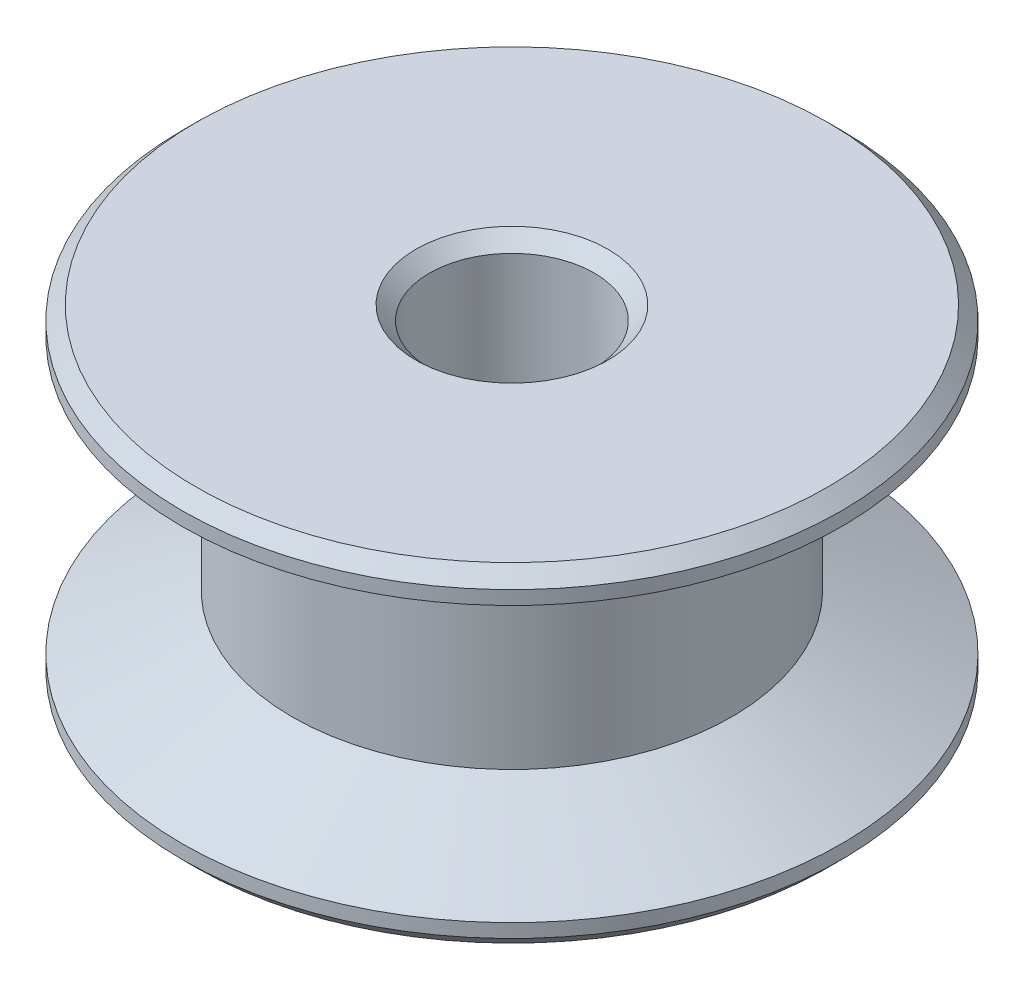
SolidWorks part; units mm, degrees
ref_plane "Front Plane" through (0, 0, 0) normal (0, 0, 1) x (1, 0, 0)
ref_plane "Top Plane" through (0, 0, 0) normal (0, 1, 0) x (1, 0, 0)
ref_plane "Right Plane" through (0, 0, 0) normal (1, 0, 0) x (0, 0, -1)
sketch "Sketch1" plane through (0, 0, 0) normal (0, 0, 1) x (1, 0, 0)
  line L0 (0, 0) -> (9.525, 0)
  line L1 (9.525, 0) -> (9.525, 0.7937)
  line L2 (9.525, 0.7937) -> (6.35, 2.3812)
  line L3 (6.35, 2.3812) -> (6.35, 7.1437)
  line L4 (6.35, 7.1437) -> (9.525, 8.7312)
  line L5 (9.525, 8.7312) -> (9.525, 9.525)
  line L6 (9.525, 9.525) -> (0, 9.525)
  line L7 (0, 9.525) -> (0, 0)
  dimension "D1" = 6.35
  dimension "D2" = 3.175
  dimension "D3" = 3.175
  dimension "D4" = 0.7937
  dimension "D5" = 1.5875
  dimension "D6" = 4.7625
  dimension "D7" = 1.5875
  dimension "D8" = 0.7937
revolve "Revolve1" add sketch "Sketch1" angle 360 about L7
sketch "Sketch2" plane through (0, 9.525, 0) normal (0, 1, 0) x (1, 0, 0)
  circle A0 centre (0, 0) radius 2.3813
  dimension "D1" = 4.7625
extrude "Cut-Extrude1" cut sketch "Sketch2" against normal through all both and the other way through all
chamfer "Chamfer1" distance 0.3969 angle 45 4 edges at (0, 0, 9.525) (-2.3813, 0, 0) (0, 9.525, 9.525) (0, 9.525, -2.3813)
